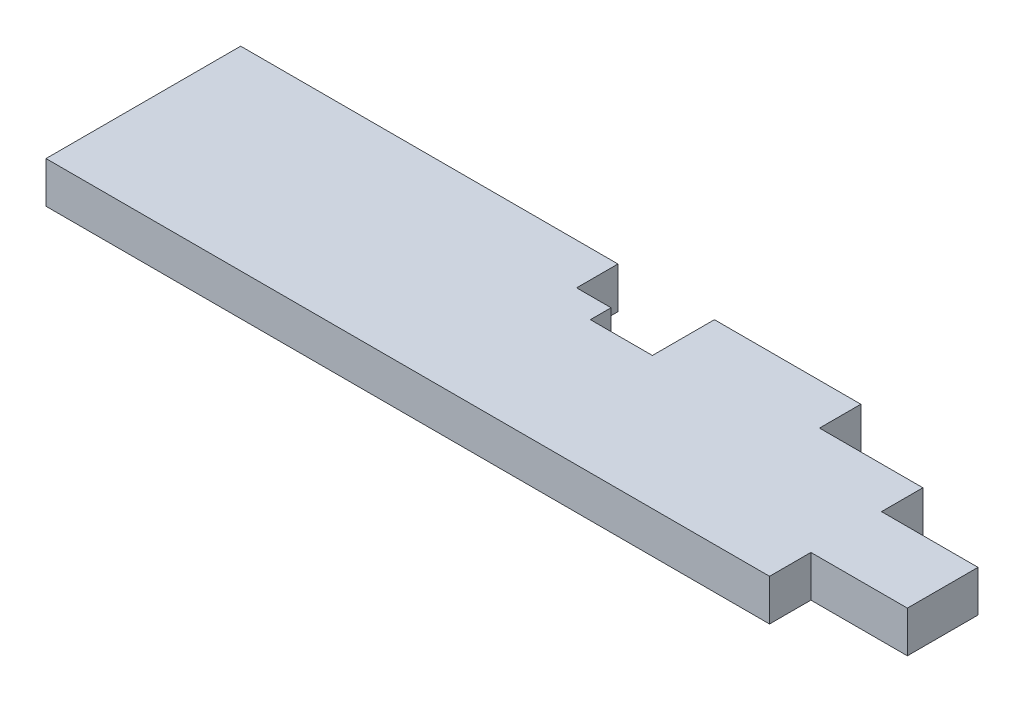
SolidWorks part; units mm, degrees
material "Pine"
ref_plane "Front Plane" through (0, 0, 0) normal (0, 0, 1) x (1, 0, 0)
ref_plane "Top Plane" through (0, 0, 0) normal (0, 1, 0) x (1, 0, 0)
ref_plane "Right Plane" through (0, 0, 0) normal (1, 0, 0) x (0, 0, -1)
sketch "Sketch1" plane through (0, 0, 0) normal (0, 1, 0) x (1, 0, 0)
  line L1 (0, 0) -> (666.75, 0)
  line L2 (0, 0) -> (0, 179.3875)
  line L3 (0, 179.3875) -> (666.75, 179.3875)
  line L4 (666.75, 0) -> (666.75, 179.3875)
  dimension "D1" = 179.3875
  dimension "D2" = 666.75
extrude "Boss-Extrude1" add sketch "Sketch1" along normal blind 38.1
sketch "Sketch2" plane through (0, 0, 0) normal (0, -1, 0) x (1, 0, 0)
  line L0 (666.75, -179.3875) -> (0, -179.3875) construction
  line L1 (666.75, -38.1) -> (755.65, -38.1)
  line L2 (666.75, -38.1) -> (666.75, -179.3875)
  line L3 (666.75, -179.3875) -> (755.65, -179.3875)
  line L4 (755.65, -38.1) -> (755.65, -179.3875)
  line L7 (666.75, 0) -> (666.75, -179.3875) construction
  line L8 (0, 0) -> (666.75, 0) construction
  dimension "D1" = 755.65
  dimension "D2" = 38.1
extrude "Boss-Extrude2" add sketch "Sketch2" against normal through all
sketch "Sketch3" plane through (0, 0, 0) normal (0, -1, 0) x (1, 0, 0)
  line L0 (755.65, -179.3875) -> (755.65, -38.1) construction
  line L1 (755.65, -179.3875) -> (571.5, -179.3875)
  line L2 (755.65, -179.3875) -> (755.65, -141.2875)
  line L3 (755.65, -141.2875) -> (571.5, -141.2875)
  line L4 (571.5, -179.3875) -> (571.5, -141.2875)
  point P7 (571.5, -160.3375)
  dimension "D1" = 38.1
  dimension "D2" = 184.15
extrude "Cut-Extrude1" cut sketch "Sketch3" against normal through all
sketch "Sketch4" plane through (0, 0, 0) normal (0, -1, 0) x (1, 0, 0)
  line L0 (436.551, -122.2375) -> (436.551, -179.3875)
  line L1 (436.551, -179.3875) -> (347.6625, -179.3875)
  line L3 (379.4125, -141.2875) -> (347.6625, -141.2875)
  line L4 (347.6625, -179.3875) -> (347.6625, -141.2875)
  line L5 (436.551, -122.2375) -> (379.4125, -122.2375)
  line L7 (436.5625, -141.2875) -> (436.551, -141.2875)
  line L8 (379.4125, -122.2375) -> (379.4125, -141.2875)
  line L9 (0, 0) -> (666.75, 0) construction
  line L10 (571.5, -179.3875) -> (0, -179.3875) construction
  line M8 (0, -179.3875) -> (571.5, -179.3875)
  dimension "D1" = 122.2375
  dimension "D2" = 347.6625
  dimension "D3" = 88.8885
  dimension "D4" = 141.2875
  dimension "D5" = 379.4125
extrude "Cut-Extrude2" cut sketch "Sketch4" against normal through all contours L5 L8 L3 L4 L0 M8
sketch "Sketch5" plane through (0, 0, 0) normal (0, -1, 0) x (1, 0, 0)
  line L1 (755.65, -141.2875) -> (666.75, -141.2875)
  line L2 (755.65, -141.2875) -> (755.65, -103.1875)
  line L3 (755.65, -103.1875) -> (666.75, -103.1875)
  line L4 (666.75, -141.2875) -> (666.75, -103.1875)
  point P7 (666.75, -122.2375)
  dimension "D1" = 103.1875
  dimension "D2" = 666.75
extrude "Cut-Extrude3" cut sketch "Sketch5" against normal through all
